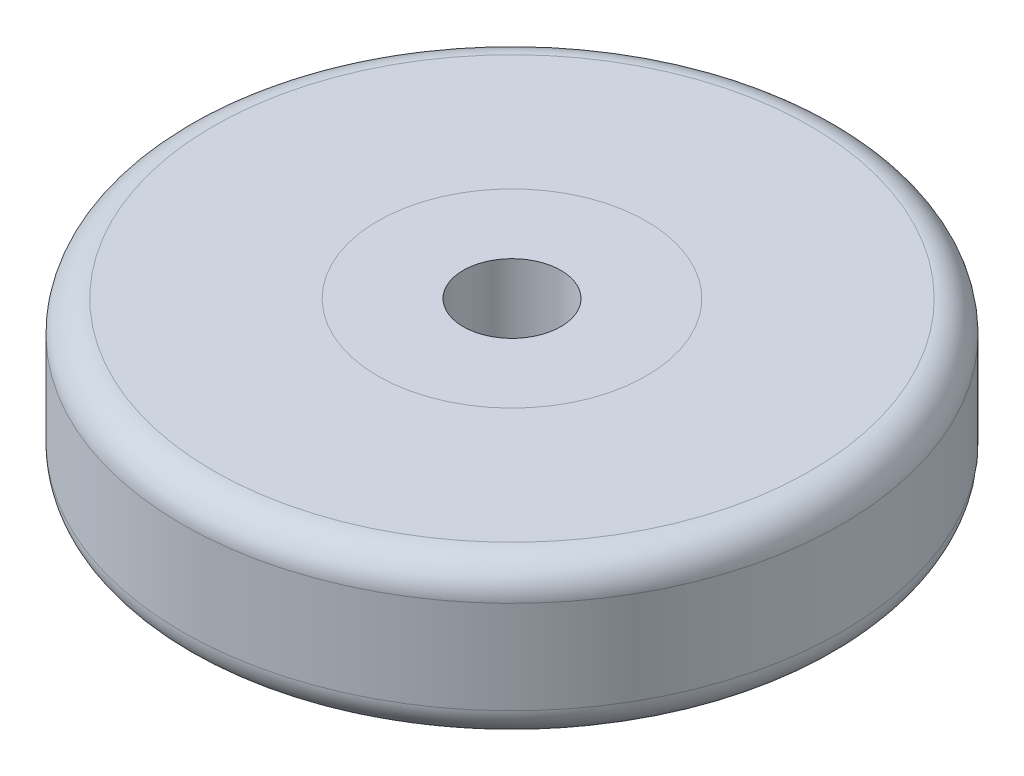
SolidWorks part; units mm, degrees
ref_plane "Front Plane" through (0, 0, 0) normal (0, 0, 1) x (1, 0, 0)
ref_plane "Top Plane" through (0, 0, 0) normal (0, 1, 0) x (1, 0, 0)
ref_plane "Right Plane" through (0, 0, 0) normal (1, 0, 0) x (0, 0, -1)
sketch "Sketch1" plane through (0, 0, 0) normal (0, 1, 0) x (1, 0, 0)
  circle A0 centre (0, 0) radius 4
  circle A1 centre (0, 0) radius 11
  dimension "D1" = 8
  dimension "D2" = 22
extrude "Boss-Extrude1" add sketch "Sketch1" along normal blind 12.7
sketch "Sketch2" plane through (0, 12.7, 0) normal (0, 1, 0) x (1, 0, 0)
  circle A0 centre (0, 0) radius 11
  circle A1 centre (0, 0) radius 27
  dimension "D1" = 54
extrude "Boss-Extrude2" add sketch "Sketch2" against normal blind 12.7 separate body
fillet "Fillet1" radius 2.54 2 edges at (0, 0, 27) (0, 12.7, 27)
